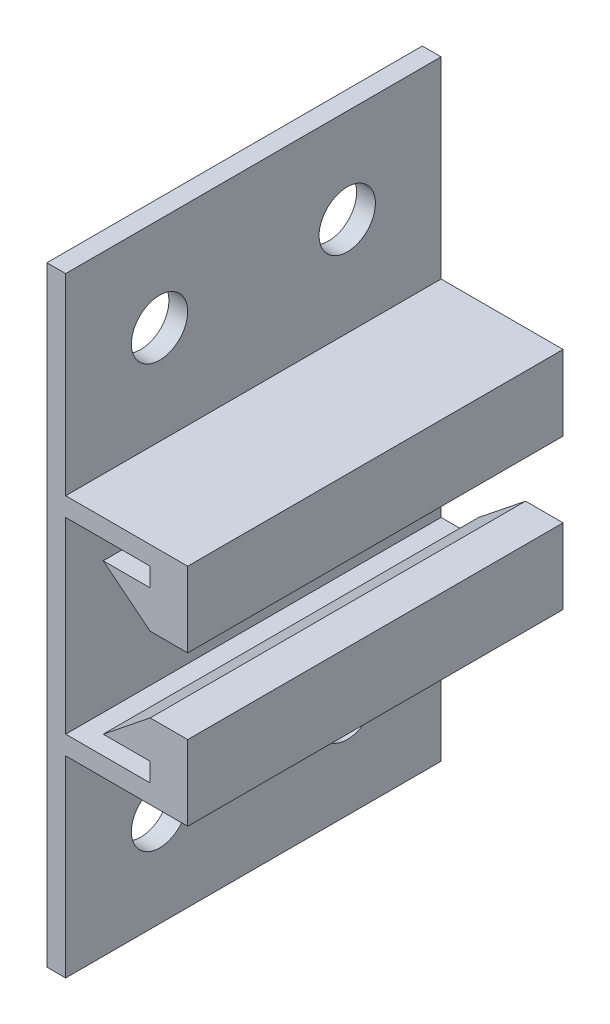
SolidWorks part; units mm, degrees
ref_plane "Front Plane" through (0, 0, 0) normal (0, 0, 1) x (1, 0, 0)
ref_plane "Top Plane" through (0, 0, 0) normal (0, 1, 0) x (1, 0, 0)
ref_plane "Right Plane" through (0, 0, 0) normal (1, 0, 0) x (0, 0, -1)
sketch "Esquisse1" plane through (0, 0, 0) normal (0, 0, 1) x (1, 0, 0)
  line L2 (1, 32.5) -> (1, 22.25)
  line L3 (1, 22.25) -> (7.5, 22.25)
  line L4 (1, 32.5) -> (0, 32.5)
  line L5 (0, 32.5) -> (0, 0)
  line L6 (7.5, 22.25) -> (7.5, 18.25)
  line L7 (7.5, 18.25) -> (5.5, 18.25)
  line L8 (5.5, 18.25) -> (3, 20.25)
  line L9 (3, 20.25) -> (5.5, 20.25)
  line L10 (5.5, 20.25) -> (5.5, 21.25)
  line L11 (5.5, 21.25) -> (1, 21.25)
  line L12 (1, 21.25) -> (1, 11.25)
  line L13 (1, 11.25) -> (5.5, 11.25)
  line L14 (5.5, 11.25) -> (5.5, 12.25)
  line L15 (5.5, 12.25) -> (3, 12.25)
  line L16 (3, 12.25) -> (5.5, 14.25)
  line L17 (5.5, 14.25) -> (7.5, 14.25)
  line L18 (7.5, 14.25) -> (7.5, 10.25)
  line L19 (7.5, 10.25) -> (1, 10.25)
  line L20 (1, 10.25) -> (1, 0)
  line L21 (1, 0) -> (0, 0)
  point P1 (4.4155, 22.3267)
  point P4 (1.4315, 11.0826)
  point P14 (1.6025, 11.4246)
  point P24 (0.9184, 12.75)
  point P25 (1.2605, 10.4413)
  point P26 (0.2771, 11.2108)
  point P27 (0, 0)
  point P28 (1.5597, 8.4746)
  point P29 (1, 25.8325)
  point P30 (1, 16.25)
  point P31 (0, 16.25)
  point P32 (9.3107, 19.098)
  point P33 (2.037, 20.25)
  point P34 (4.4908, 18.25)
  dimension "D1" = 32.5
  dimension "D2" = 1
  dimension "D3" = 10
  dimension "D4" = 1
  dimension "D5" = 1
  dimension "D6" = 6.5
  dimension "D7" = 4
  dimension "D8" = 2
  dimension "D9" = 2
  dimension "D10" = 2
extrude "Boss.-Extru.1" add sketch "Esquisse1" along normal blind 20
sketch "Esquisse2" plane through (1, 0, 0) normal (1, 0, 0) x (0, 0, -1)
  line L0 (-20, 32.5) -> (0, 32.5) construction
  line L1 (-20, 22.25) -> (-20, 32.5) construction
  line L2 (-20, 0) -> (0, 0) construction
  circle A0 centre (-15, 27.5) radius 1.5
  circle A1 centre (-15, 5) radius 1.5
  point P10 (-14.2637, 5)
  dimension "D1" = 3
  dimension "D2" = 5
  dimension "D3" = 5
  dimension "D4" = 5
extrude "Enlèv. mat.-Extru.1" cut sketch "Esquisse2" against normal through all
pattern_linear "Répétition linéaire1" count 2 spacing 10 along (0, 0, -1) of "Enlèv. mat.-Extru.1"
